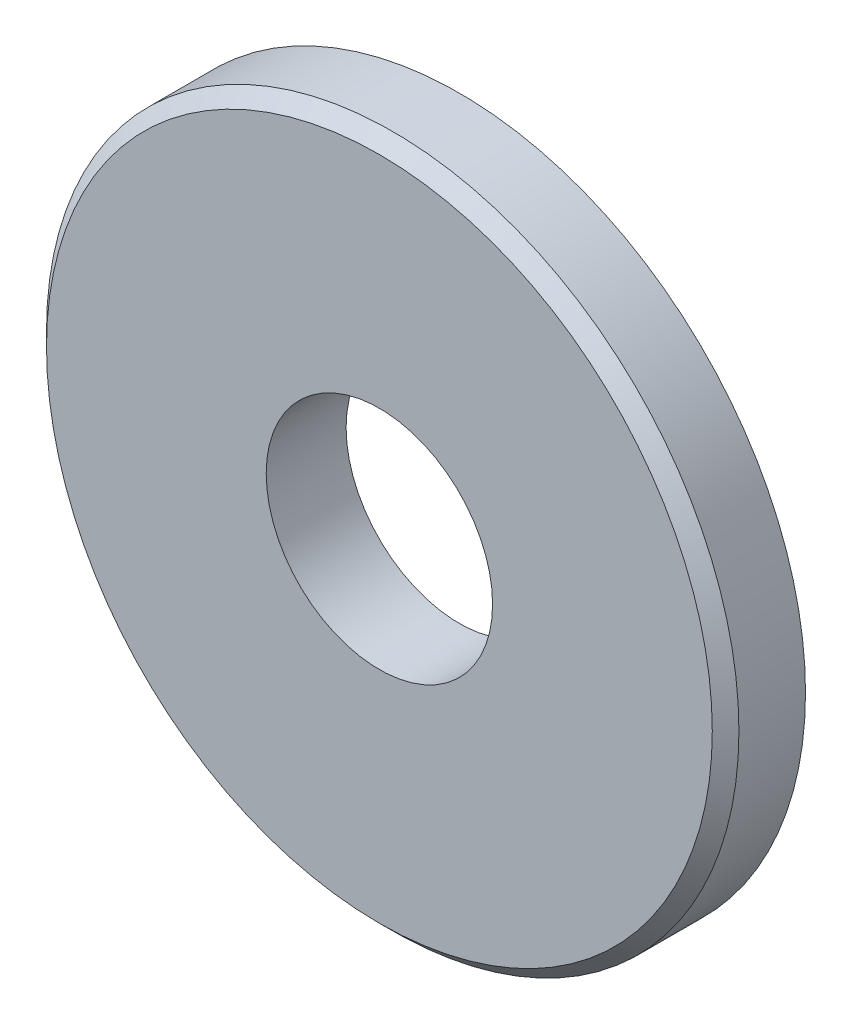
SolidWorks part; units mm, degrees
ref_plane "Alzado" through (0, 0, 0) normal (0, 0, 1) x (1, 0, 0)
ref_plane "Planta" through (0, 0, 0) normal (0, 1, 0) x (1, 0, 0)
ref_plane "Vista lateral" through (0, 0, 0) normal (1, 0, 0) x (0, 0, -1)
sketch "Croquis1" plane through (0, 0, 0) normal (0, 0, 1) x (1, 0, 0)
  circle A0 centre (0, 0) radius 4.25
  circle A1 centre (0, 0) radius 13
  dimension "D1" = 8.5
  dimension "D2" = 26
extrude "Saliente-Extruir1" add sketch "Croquis1" along normal blind 3
chamfer "Chaflán1" distance 0.5 angle 45 1 edges at (13, 0, 3)
